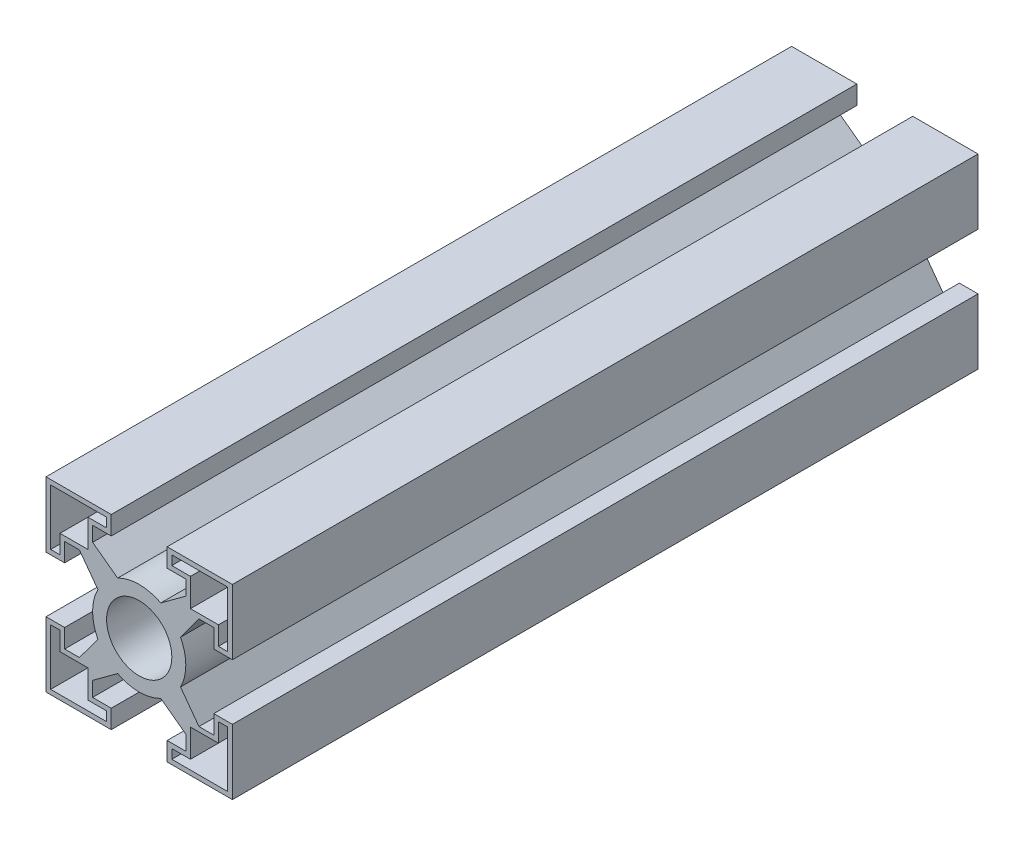
SolidWorks part; units mm, degrees
ref_plane "Plan de face" through (0, 0, 0) normal (0, 0, 1) x (1, 0, 0)
ref_plane "Plan de dessus" through (0, 0, 0) normal (0, 1, 0) x (1, 0, 0)
ref_plane "Plan de droite" through (0, 0, 0) normal (1, 0, 0) x (0, 0, -1)
sketch "Esquisse1" plane through (0, 0, 0) normal (0, 0, 1) x (1, 0, 0)
  line L5 (-5, 5) -> (-5, 1.5)
  line L22 (5, -5) -> (-5, -5) construction
  line L23 (5, -5) -> (5, 5) construction
  line L24 (5, 5) -> (-5, 5) construction
  line L25 (-5, -5) -> (-5, 5) construction
  line L26 (5, -5) -> (-5, 5) construction
  line L27 (5, 5) -> (-5, -5) construction
  line L28 (-5, 1.5) -> (-4, 1.5)
  line L29 (-4, 1.5) -> (-4, 2.5)
  line L30 (-4, 2.5) -> (-2.5, 2.5)
  line L79 (-2.5, 2.5) -> (-2.5, 4)
  line L80 (-2.5, 4) -> (-1.5, 4)
  line L82 (-1.5, 4) -> (-1.5, 5)
  line L85 (-1.5, 5) -> (-5, 5)
  line L86 (-4.75, 4.75) -> (-4.75, 1.75)
  line L87 (-4.75, 1.75) -> (-4.25, 1.75)
  line L88 (-4.25, 1.75) -> (-4.25, 2.75)
  line L89 (-4.25, 2.75) -> (-2.75, 2.75)
  line L90 (-2.75, 2.75) -> (-2.75, 4.25)
  line L92 (-2.75, 4.25) -> (-1.75, 4.25)
  line L93 (-1.75, 4.25) -> (-1.75, 4.75)
  line L94 (-1.75, 4.75) -> (-4.75, 4.75)
  line L95 (5, 5) -> (1.5, 5)
  line L96 (1.5, 5) -> (1.5, 4)
  line L97 (1.5, 4) -> (2.5, 4)
  line L98 (2.5, 4) -> (2.5, 2.5)
  line L99 (2.5, 2.5) -> (4, 2.5)
  line L100 (4, 2.5) -> (4, 1.5)
  line L101 (4, 1.5) -> (5, 1.5)
  line L102 (5, 1.5) -> (5, 5)
  line L103 (4.75, 4.75) -> (1.75, 4.75)
  line L104 (1.75, 4.75) -> (1.75, 4.25)
  line L105 (1.75, 4.25) -> (2.75, 4.25)
  line L106 (2.75, 4.25) -> (2.75, 2.75)
  line L107 (2.75, 2.75) -> (4.25, 2.75)
  line L108 (4.25, 2.75) -> (4.25, 1.75)
  line L109 (4.25, 1.75) -> (4.75, 1.75)
  line L110 (4.75, 1.75) -> (4.75, 4.75)
  line L111 (5, -5) -> (5, -1.5)
  line L112 (5, -1.5) -> (4, -1.5)
  line L113 (4, -1.5) -> (4, -2.5)
  line L114 (4, -2.5) -> (2.5, -2.5)
  line L115 (2.5, -2.5) -> (2.5, -4)
  line L116 (2.5, -4) -> (1.5, -4)
  line L117 (1.5, -4) -> (1.5, -5)
  line L118 (1.5, -5) -> (5, -5)
  line L119 (4.75, -4.75) -> (4.75, -1.75)
  line L120 (4.75, -1.75) -> (4.25, -1.75)
  line L121 (4.25, -1.75) -> (4.25, -2.75)
  line L122 (4.25, -2.75) -> (2.75, -2.75)
  line L123 (2.75, -2.75) -> (2.75, -4.25)
  line L124 (2.75, -4.25) -> (1.75, -4.25)
  line L125 (1.75, -4.25) -> (1.75, -4.75)
  line L126 (1.75, -4.75) -> (4.75, -4.75)
  line L127 (-5, -5) -> (-1.5, -5)
  line L128 (-1.5, -5) -> (-1.5, -4)
  line L129 (-1.5, -4) -> (-2.5, -4)
  line L130 (-2.5, -4) -> (-2.5, -2.5)
  line L131 (-2.5, -2.5) -> (-4, -2.5)
  line L132 (-4, -2.5) -> (-4, -1.5)
  line L133 (-4, -1.5) -> (-5, -1.5)
  line L134 (-5, -1.5) -> (-5, -5)
  line L135 (-4.75, -4.75) -> (-1.75, -4.75)
  line L136 (-1.75, -4.75) -> (-1.75, -4.25)
  line L137 (-1.75, -4.25) -> (-2.75, -4.25)
  line L138 (-2.75, -4.25) -> (-2.75, -2.75)
  line L139 (-2.75, -2.75) -> (-4.25, -2.75)
  line L140 (-4.25, -2.75) -> (-4.25, -1.75)
  line L141 (-4.25, -1.75) -> (-4.75, -1.75)
  line L142 (-4.75, -1.75) -> (-4.75, -4.75)
  line L143 (-3.2071, 2.5) -> (-2.2167, 1.156)
  line L144 (-2.5, 3.2071) -> (-1.156, 2.2167)
  line L145 (-2.2167, 1.156) -> (-1.156, 2.2167) construction
  line L146 (-2.5, 3.2071) -> (-3.2071, 2.5) construction
  line L147 (3.2071, 2.5) -> (2.2167, 1.156)
  line L148 (2.5, 3.2071) -> (1.156, 2.2167)
  line L149 (2.5, -3.2071) -> (1.156, -2.2167)
  line L150 (3.2071, -2.5) -> (2.2167, -1.156)
  line L151 (-3.2071, -2.5) -> (-2.2167, -1.156)
  line L152 (-2.5, -3.2071) -> (-1.156, -2.2167)
  circle A2 centre (0, 0) radius 1.75
  circle A3 centre (0, 0) radius 2.5
  point P73 (0, 0)
  point P78 (-2.8536, 2.8536)
  point P79 (-1.6863, 1.6863)
  point P91 (0, 0)
  dimension "D2" = 3.5
  dimension "D3" = 10
  dimension "D1" = 5
  dimension "D4" = 3.5
  dimension "D5" = 1
  dimension "D6" = 1.5
  dimension "D7" = 0.25
  dimension "D8" = 4
  dimension "D9" = 1
  dimension "D10" = 1.5
extrude "Boss.-Extru.1" add sketch "Esquisse1" along normal blind 40
